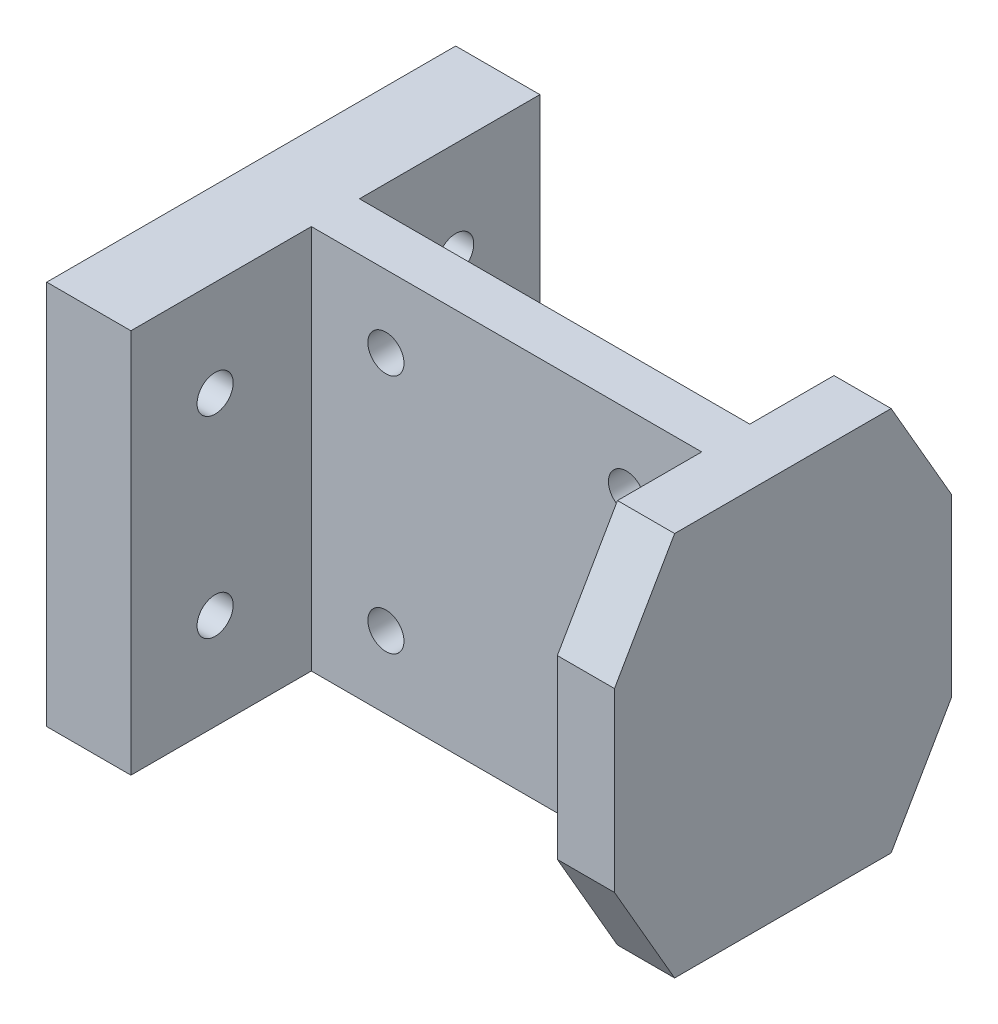
SolidWorks part; units mm, degrees
ref_plane "Спереди" through (0, 0, 0) normal (0, 0, 1) x (1, 0, 0)
ref_plane "Сверху" through (0, 0, 0) normal (0, 1, 0) x (1, 0, 0)
ref_plane "Справа" through (0, 0, 0) normal (1, 0, 0) x (0, 0, -1)
sketch "Эскиз1" plane through (0, 0, 0) normal (0, 0, 1) x (1, 0, 0)
  line L0 (0, 0) -> (36, 0)
  line L1 (0, 0) -> (0, 32)
  line L2 (36, 0) -> (36, 32)
  line L3 (0, 32) -> (36, 32)
  line L4 (18, 32) -> (18, 0) construction
  line L5 (36, 16) -> (0, 16) construction
  line L6 (8, 26) -> (8, 6) construction
  line L7 (8, 26) -> (28, 26) construction
  line L8 (28, 26) -> (28, 6) construction
  line L9 (28, 6) -> (8, 6) construction
  line L10 (8, 16) -> (28, 16) construction
  line L11 (18, 26) -> (18, 6) construction
  circle A0 centre (8, 26) radius 1.5
  circle A1 centre (28, 26) radius 1.5
  circle A2 centre (8, 6) radius 1.5
  circle A3 centre (28, 6) radius 1.5
  dimension "D1" = 20
  dimension "D2" = 20
  dimension "D3" = 3
  dimension "D4" = 3
  dimension "D5" = 3
  dimension "D6" = 3
  dimension "D7" = 32
  dimension "D8" = 36
extrude "Бобышка-Вытянуть1" add sketch "Эскиз1" along normal blind 4
sketch "Эскиз6" plane through (0, 32, 0) normal (0, 1, 0) x (1, 0, 0)
  line L0 (-5.2, -4) -> (-5.2, 24.8582) construction
  line L1 (36, -4) -> (0, -4) construction
  line L2 (36, -4) -> (36, 0) construction
  line L3 (-7.2, -4) -> (-7.2, 26.2382) construction
  dimension "D1" = 41.2
  dimension "D2" = 2
sketch "Эскиз7" plane through (0, 32, 0) normal (0, 1, 0) x (1, 0, 0)
  line L0 (0, 0) -> (-1.2, 0)
  line L1 (-1.2, 0) -> (-1.2, 15)
  line L3 (0, -4) -> (-1.2, -4)
  line L4 (-1.2, -4) -> (-1.2, -19)
  line L5 (-1.2, -19) -> (-5.2, -19)
  line L6 (-5.2, -19) -> (-5.2, 15)
  line L7 (-5.2, 15) -> (-1.2, 15)
  line L8 (-5.2, -4) -> (-5.2, 24.8582) construction
  line L9 (0, -4) -> (0, 0)
  dimension "D1" = 4
  dimension "D2" = 15
  dimension "D3" = 15
extrude "Бобышка-Вытянуть2" add sketch "Эскиз7" against normal up to surface (32 mm away) up to face at (18, 0, 2)
sketch "Эскиз8" plane through (-1.2, 0, 0) normal (1, 0, 0) x (0, 0, -1)
  line L0 (8, 24) -> (-12, 24) construction
  line L3 (8, 24) -> (8, 8) construction
  line L4 (-12, 24) -> (-12, 8) construction
  line L5 (8, 8) -> (-12, 8) construction
  line L6 (-4, 0) -> (-4, 32) construction
  line L7 (-4, 0) -> (-19, 0) construction
  line L8 (-19, 32) -> (-4, 32) construction
  circle A0 centre (8, 24) radius 1.5
  circle A1 centre (8, 8) radius 1.5
  circle A2 centre (-12, 8) radius 1.5
  circle A3 centre (-12, 24) radius 1.5
  dimension "D7" = 3
  dimension "D8" = 3
  dimension "D9" = 3
  dimension "D10" = 3
  dimension "D1" = 20
  dimension "D2" = 8
  dimension "D3" = 8
  dimension "D4" = 16
  dimension "D5" = 8
  dimension "D6" = 8
extrude "Вырез-Вытянуть1" cut sketch "Эскиз8" against normal through all
sketch "Sketch1" plane through (36, 0, 0) normal (1, 0, 0) x (0, 0, -1)
  line L4 (0, 0) -> (0, 32)
  line L5 (0, 32) -> (-4, 32)
  line L6 (-4, 32) -> (-4, 0)
  line L7 (-4, 0) -> (0, 0)
  line L8 (0, 0) -> (0, 32)
  line L9 (0, 32) -> (-4, 32)
  line L10 (-4, 32) -> (-4, 0)
  line L11 (-4, 0) -> (0, 0)
  dimension "D1" = 0
extrude "Boss-Extrude1" add sketch "Sketch1" along normal blind 3
sketch "Sketch2" plane through (0, 0, 0) normal (0, 0, -1) x (-1, 0, 0)
  line L0 (-39, 32) -> (-34, 32)
  line L1 (-39, 32) -> (-39, 0)
  line L2 (-34, 32) -> (-34, 0)
  line L3 (-39, 0) -> (-34, 0)
  line L4 (-39, 32) -> (1.2, 32) construction
  line L5 (1.2, 0) -> (-39, 0) construction
  dimension "D1" = 5
extrude "Boss-Extrude2" add sketch "Sketch2" along normal blind 12
sketch "Sketch3" plane through (39, 0, 0) normal (1, 0, 0) x (0, 0, -1)
  line L0 (0, 0) -> (0, 32) construction
  line L1 (0, 0) -> (0, 32) construction
  line L2 (0, 32) -> (7, 32) construction
  line L3 (12, 32) -> (-4, 32) construction
  line L4 (7, 32) -> (12, 23.3397) construction
  line L5 (12, 32) -> (12, 0) construction
  line L6 (0, 16) -> (12, 16) construction
  line L7 (12, 23.3397) -> (12, 8.6603) construction
  line L8 (7, 0) -> (12, 8.6603) construction
  line L9 (7, 32) -> (12, 32)
  line L10 (12, 32) -> (12, 23.3397)
  line L11 (12, 23.3397) -> (7, 32)
  line L12 (7, 0) -> (12, 8.6603) construction
  line L13 (0, 0) -> (7, 0) construction
  line L14 (12, 8.6603) -> (7, 0)
  line L15 (12, 0) -> (12, 8.6603)
  line L16 (7, 0) -> (12, 0)
  dimension "D1" = 120
  dimension "D2" = 7
extrude "Cut-Extrude1" cut sketch "Sketch3" against normal up to surface (5 mm away) up to face at (34, 16, -6)
sketch "Sketch6" plane through (39, 0, 0) normal (1, 0, 0) x (0, 0, -1)
  line L0 (7, 32) -> (0, 32) construction
  line L1 (7, 32) -> (0, 32) construction
  line L2 (7, 0) -> (0, 0) construction
  line L3 (7, 0) -> (0, 0) construction
  line L4 (0, 32) -> (0, 0) construction
  line L5 (-4, 32) -> (0, 32) construction
  line L6 (-4, 0) -> (0, 0) construction
  line L7 (-2, 32) -> (-2, 0) construction
  line L8 (12, 8.6603) -> (7, 0) construction
  line L9 (7, 32) -> (12, 23.3397) construction
  line L10 (12, 23.3397) -> (12, 8.6603) construction
  line L11 (7, 32) -> (12, 23.3397) construction
  line L12 (12, 23.3397) -> (12, 8.6603) construction
  line L13 (12, 8.6603) -> (7, 0) construction
  line L14 (-16, 8.6603) -> (-11, 0)
  line L15 (-16, 23.3397) -> (-16, 8.6603)
  line L16 (-11, 32) -> (-16, 23.3397)
  line L17 (-11, 32) -> (-4, 32)
  line L18 (-4, 32) -> (-4, 0)
  line L19 (-4, 0) -> (-11, 0)
extrude "Boss-Extrude5" add sketch "Sketch6" against normal blind 5
sketch "Sketch7" plane through (-1.2, 0, 0) normal (1, 0, 0) x (0, 0, -1)
  line L4 (0, 0) -> (15, 0)
  line L5 (15, 0) -> (15, 32)
  line L6 (15, 32) -> (0, 32)
  line L7 (0, 32) -> (0, 0)
  line L8 (0, 0) -> (15, 0)
  line L9 (15, 0) -> (15, 32)
  line L10 (15, 32) -> (0, 32)
  line L11 (0, 32) -> (0, 0)
  line L12 (-19, 0) -> (-4, 0)
  line L13 (-4, 0) -> (-4, 32)
  line L14 (-4, 32) -> (-19, 32)
  line L15 (-19, 32) -> (-19, 0)
  line L16 (-19, 0) -> (-4, 0)
  line L17 (-4, 0) -> (-4, 32)
  line L18 (-4, 32) -> (-19, 32)
  line L19 (-19, 32) -> (-19, 0)
  circle A0 centre (-12, 24) radius 1.5 construction
  circle A1 centre (-12, 8) radius 1.5 construction
  circle A2 centre (8, 24) radius 1.5 construction
  circle A3 centre (8, 8) radius 1.5 construction
  circle A4 centre (-12, 24) radius 1.5
  circle A5 centre (-12, 8) radius 1.5
  circle A6 centre (8, 24) radius 1.5
  circle A7 centre (8, 8) radius 1.5
  dimension "D1" = 0
  dimension "D2" = 0
extrude "Boss-Extrude6" add sketch "Sketch7" along normal blind 3
sketch "Sketch8" plane through (34, 0, 0) normal (-1, 0, 0) x (0, 0, 1)
  line L0 (-12, 23.3397) -> (-12, 8.6603) construction
  line L1 (-12, 8.6603) -> (-7, 0) construction
  line L2 (-7, 0) -> (0, 0) construction
  line L3 (0, 0) -> (0, 32) construction
  line L4 (0, 32) -> (-7, 32) construction
  line L5 (-7, 32) -> (-12, 23.3397) construction
  line L6 (4, 32) -> (4, 0) construction
  line L7 (4, 0) -> (11, 0) construction
  line L8 (11, 0) -> (16, 8.6603) construction
  line L9 (16, 8.6603) -> (16, 23.3397) construction
  line L10 (16, 23.3397) -> (11, 32) construction
  line L11 (11, 32) -> (4, 32) construction
  line L12 (-12, 23.3397) -> (-12, 8.6603)
  line L13 (-12, 8.6603) -> (-7, 0)
  line L14 (-7, 0) -> (0, 0)
  line L15 (0, 0) -> (0, 32)
  line L16 (0, 32) -> (-7, 32)
  line L17 (-7, 32) -> (-12, 23.3397)
  line L18 (4, 32) -> (4, 0)
  line L19 (4, 0) -> (11, 0)
  line L20 (11, 0) -> (16, 8.6603)
  line L21 (16, 8.6603) -> (16, 23.3397)
  line L22 (16, 23.3397) -> (11, 32)
  line L23 (11, 32) -> (4, 32)
extrude "Cut-Extrude2" cut sketch "Sketch8" against normal blind 0.25
